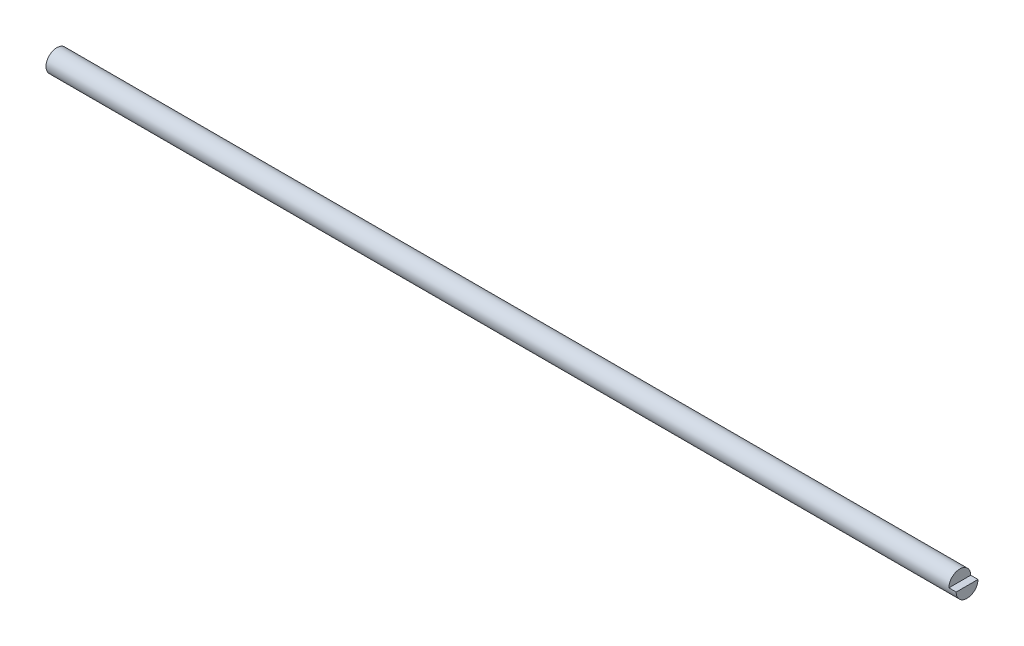
SolidWorks part; units mm, degrees
ref_plane "Front Plane" through (0, 0, 0) normal (0, 0, 1) x (1, 0, 0)
ref_plane "Top Plane" through (0, 0, 0) normal (0, 1, 0) x (1, 0, 0)
ref_plane "Right Plane" through (0, 0, 0) normal (1, 0, 0) x (0, 0, -1)
sketch "Sketch1" plane through (0, 0, 0) normal (1, 0, 0) x (0, 0, -1)
  circle A0 centre (0, 0) radius 3.81
  dimension "D1" = 7.62
extrude "Boss-Extrude1" add sketch "Sketch1" along normal blind 317.5
sketch "Sketch2" plane through (317.5, 0, 0) normal (1, 0, 0) x (0, 0, -1)
  line L0 (0, 0) -> (-3.81, 0)
  line L1 (-3.81, 0) -> (3.81, 0)
  circle A1 centre (0, 0) radius 3.81 construction
  arc A2 (-3.81, 0) -> (3.81, 0) centre (0, 0) cw
  point P6 (-33.23, -84.1026)
  circle M1 centre (0, 0) radius 3.81
extrude "Cut-Extrude1" cut sketch "Sketch2" against normal blind 2.54 contours L0 L1 M1
